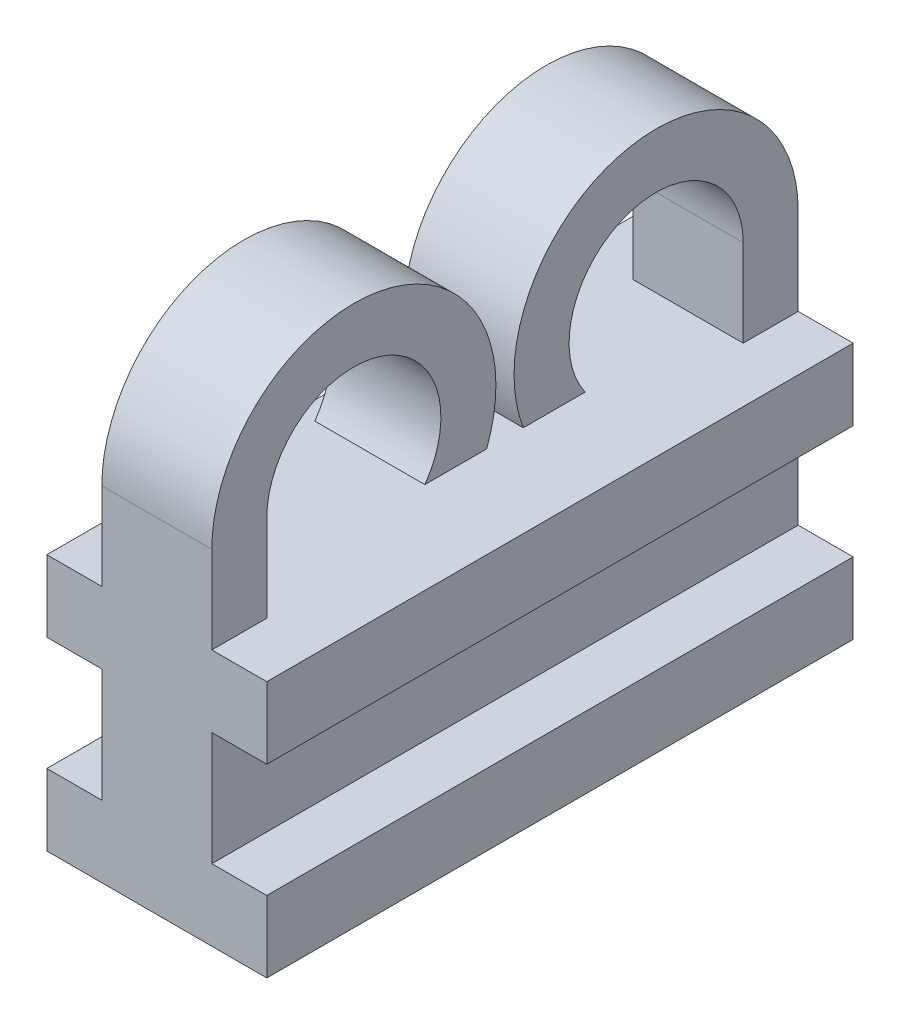
SolidWorks part; units mm, degrees
ref_plane "Front Plane" through (0, 0, 0) normal (0, 0, 1) x (1, 0, 0)
ref_plane "Top Plane" through (0, 0, 0) normal (0, 1, 0) x (1, 0, 0)
ref_plane "Right Plane" through (0, 0, 0) normal (1, 0, 0) x (0, 0, -1)
sketch "Sketch1" plane through (0, 0, 0) normal (1, 0, 0) x (0, 0, -1)
  line L0 (-6.4978, 0) -> (-6.4978, 2.375)
  line L1 (-7.9978, 0) -> (7.9978, 0)
  line L2 (-7.9978, 0) -> (-7.9978, -2)
  line L3 (-7.9978, -2) -> (7.9978, -2)
  line L4 (7.9978, 0) -> (7.9978, -2)
  line L5 (-2.1864, 1) -> (-0.5, 1)
  line L6 (-7.9978, 2.375) -> (-7.9978, 0)
  line L7 (7.9978, 0) -> (7.9978, 2.375)
  line L8 (0.5, 1) -> (2.1864, 1)
  line L9 (6.4978, 2.375) -> (6.4978, 0)
  line L11 (7.9978, -2) -> (-7.9978, -2)
  line L12 (7.9978, -2) -> (7.9978, -5)
  line L13 (7.9978, -5) -> (-7.9978, -5)
  line L14 (-7.9978, -2) -> (-7.9978, -5)
  line L15 (7.9978, -5) -> (-7.9978, -5)
  line L16 (7.9978, -5) -> (7.9978, -7)
  line L17 (7.9978, -7) -> (-7.9978, -7)
  line L18 (-7.9978, -5) -> (-7.9978, -7)
  arc A0 (-6.4978, 2.375) -> (-2.1864, 1) centre (-4.1228, 2.375) cw
  arc A1 (-0.5, 1) -> (-7.9978, 2.375) centre (-4.1228, 2.375) ccw
  arc A2 (7.9978, 2.375) -> (0.5, 1) centre (4.1228, 2.375) ccw
  arc A3 (2.1864, 1) -> (6.4978, 2.375) centre (4.1228, 2.375) cw
  point P4 (0, 0)
  dimension "D4" = 2.375
  dimension "D5" = 1
  dimension "D1" = 2
  dimension "D2" = 1
  dimension "D3" = 1.5
  dimension "D6" = 2.375
  dimension "D7" = 3
  dimension "D8" = 2
extrude "Boss-Extrude1" add sketch "Sketch1" along normal blind 3 contours L5 A1 L6 L1 L0 A0 | L4 L1 L2 L3 | L8 A3 L9 L1 L7 A2 | L12 L11 L14 L13 | L16 L15 L18 L17
ref_plane "Plane1" through (1.5, 0, 0) normal (1, 0, 0) x (0, 0, -1)
sketch "Sketch4" plane through (1.5, 0, 0) normal (1, 0, 0) x (0, 0, -1)
  line L0 (7.9978, 2.375) -> (7.9978, -7) construction
  line L1 (7.9978, 0) -> (-7.9978, 0)
  line L2 (7.9978, 0) -> (7.9978, -1.95)
  line L3 (7.9978, -1.95) -> (-7.9978, -1.95)
  line L4 (-7.9978, 0) -> (-7.9978, -1.95)
  line L5 (-7.9978, 2.375) -> (-7.9978, -7) construction
  line L6 (-6.4978, 0) -> (6.4978, 0) construction
  line L7 (7.9978, -7) -> (-7.9978, -7)
  line L8 (7.9978, -7) -> (7.9978, -5.05)
  line L9 (7.9978, -5.05) -> (-7.9978, -5.05)
  line L10 (-7.9978, -7) -> (-7.9978, -5.05)
  dimension "D1" = 1.95
  dimension "D2" = 1.95
extrude "Boss-Extrude2" add sketch "Sketch4" along normal mid plane 6
